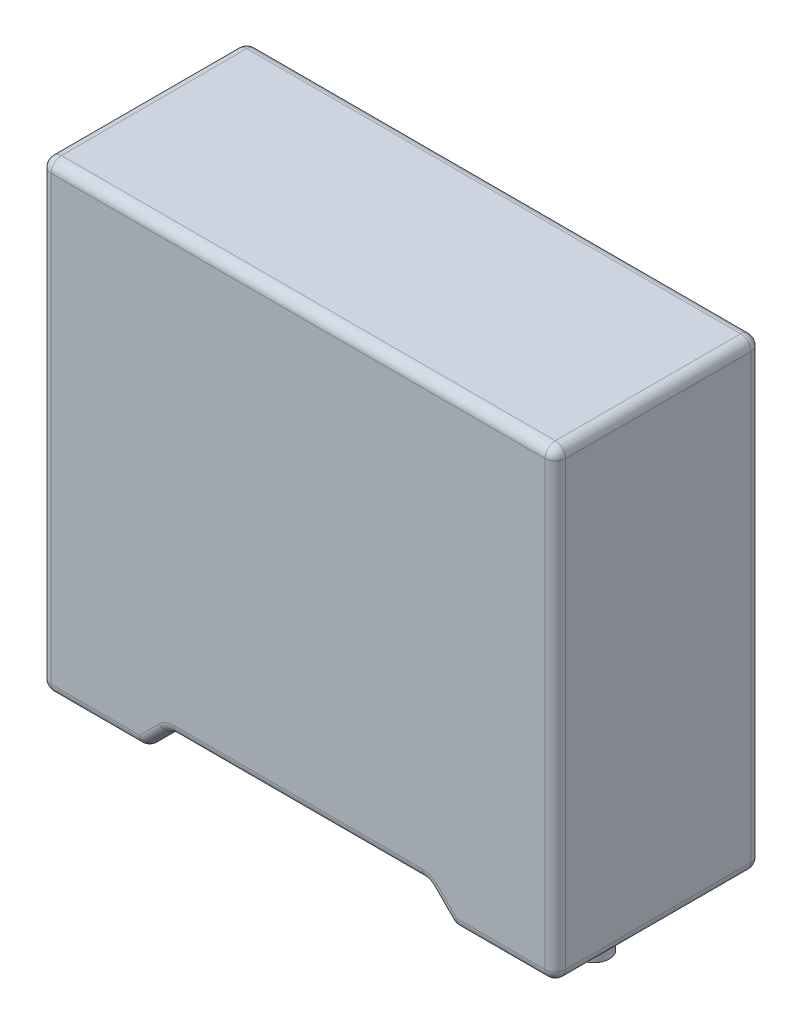
SolidWorks part; units mm, degrees
ref_plane "Front Plane" through (0, 0, 0) normal (0, 0, 1) x (1, 0, 0)
ref_plane "Top Plane" through (0, 0, 0) normal (0, 1, 0) x (1, 0, 0)
ref_plane "Right Plane" through (0, 0, 0) normal (1, 0, 0) x (0, 0, -1)
sketch "Sketch1" plane through (0, 0, 0) normal (0, 1, 0) x (1, 0, 0)
  line L0 (5, -2) -> (-5, 2) construction
  line L1 (-5, 2) -> (5, 2)
  line L2 (-5, 2) -> (-5, -2)
  line L3 (-5, -2) -> (5, -2)
  line L4 (5, 2) -> (5, -2)
  dimension "D1" = 10
  dimension "D2" = 4
extrude "Boss-Extrude1" add sketch "Sketch1" along normal blind 9
sketch "Sketch2" plane through (0, 0, 2) normal (0, 0, 1) x (1, 0, 0)
  line L0 (-3, 0) -> (-2.5, 0.5)
  line L1 (-5, 0) -> (5, 0) construction
  line L2 (-2.5, 0.5) -> (2.5, 0.5)
  line L3 (2.5, 0.5) -> (3, 0)
  line L4 (3, 0) -> (3, -1.5)
  line L5 (3, -1.5) -> (-3, -1.5)
  line L6 (-3, -1.5) -> (-3, 0)
  line L7 (0, 0) -> (0, 0.5) construction
  dimension "D1" = 2
  dimension "D2" = 0.5
  dimension "D3" = 45
  dimension "D4" = 2
extrude "Cut-Extrude1" cut sketch "Sketch2" against normal through all
sketch "Sketch3" plane through (0, 0, 0) normal (0, -1, 0) x (1, 0, 0)
  line L0 (-3.75, 0) -> (3.75, 0) construction
  circle A0 centre (3.75, 0) radius 0.3
  circle A1 centre (-3.75, 0) radius 0.3
  dimension "D1" = 0.6
  dimension "D2" = 7.5
extrude "Boss-Extrude2" add sketch "Sketch3" along normal blind 1
fillet "Fillet1" radius 0.2 24 edges at (5, 0, 0) (2.75, 0.25, -2) (4, 0, -2) (5, 4.5, -2) (-4, 0, -2) (-2.75, 0.25, -2) (0, 0.5, -2) (-5, 4.5, -2) (-5, 0, 0) (0, 9, -2) (5, 9, 0) (-5, 9, 0) (-5, 4.5, 2) (0, 9, 2) (5, 4.5, 2) (4, 0, 2) (2.75, 0.25, 2) (0, 0.5, 2) (-2.75, 0.25, 2) (-4, 0, 2) (3, 0, 0) (-3, 0, 0) (-2.5, 0.5, 0) (2.5, 0.5, 0)
